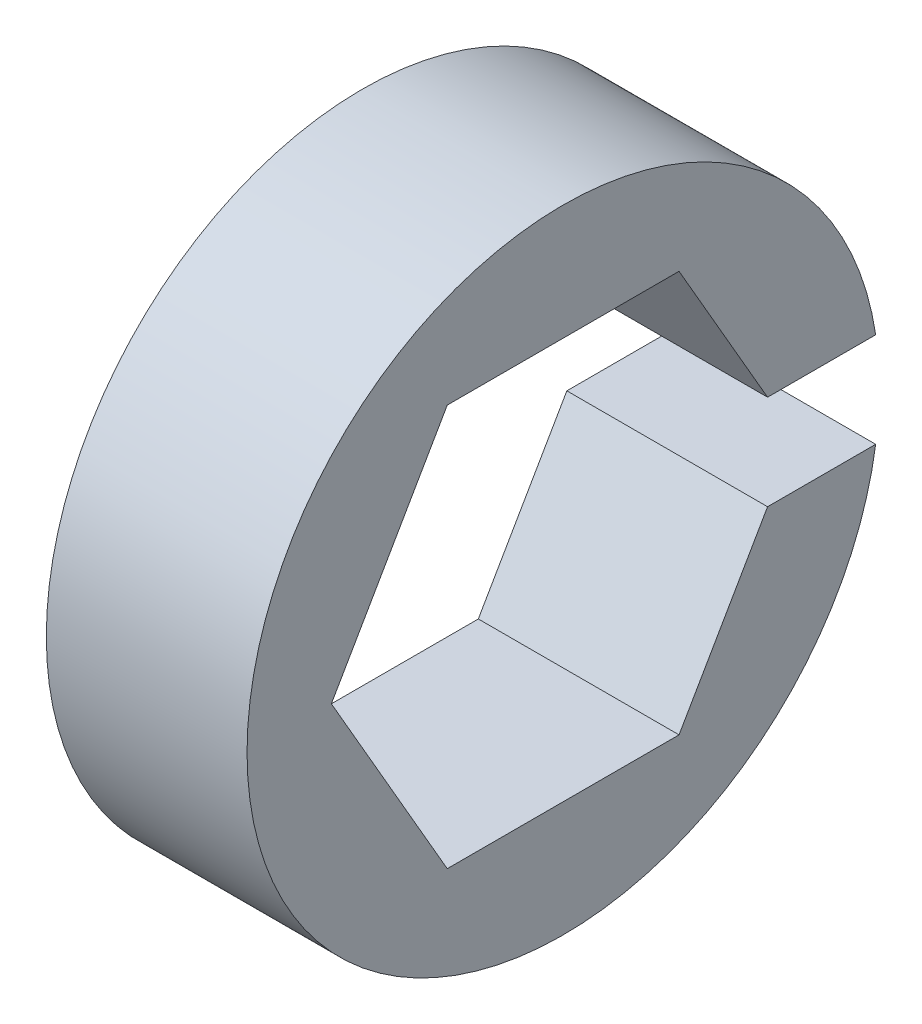
SolidWorks part; units mm, degrees
ref_plane "Front Plane" through (0, 0, 0) normal (0, 0, 1) x (1, 0, 0)
ref_plane "Top Plane" through (0, 0, 0) normal (0, 1, 0) x (1, 0, 0)
ref_plane "Right Plane" through (0, 0, 0) normal (1, 0, 0) x (0, 0, -1)
sketch "Sketch1" plane through (0, 0, 0) normal (1, 0, 0) x (0, 0, -1)
  line L1 (7.3323, 0) -> (3.6662, 6.35)
  line L2 (3.6662, 6.35) -> (-3.6662, 6.35)
  line L3 (-3.6662, 6.35) -> (-7.3323, 0)
  line L4 (-7.3323, 0) -> (-3.6662, -6.35)
  line L5 (-3.6662, -6.35) -> (3.6662, -6.35)
  line L6 (3.6662, -6.35) -> (7.3323, 0)
  circle A0 centre (0, 0) radius 10
  circle A1 centre (0, 0) radius 6.35 construction
  dimension "D2" = 20
  dimension "D1" = 12.7
extrude "Boss-Extrude1" add sketch "Sketch1" along normal blind 6.35
sketch "Sketch2" plane through (6.35, 0, 0) normal (1, 0, 0) x (0, 0, -1)
  line L1 (5.8102, 1.5) -> (11.4103, 1.5)
  line L2 (5.8102, 1.5) -> (5.8102, -1.5)
  line L3 (5.8102, -1.5) -> (11.4103, -1.5)
  line L4 (11.4103, 1.5) -> (11.4103, -1.5)
  point P4 (11.4103, 0)
  dimension "D1" = 3
extrude "Cut-Extrude1" cut sketch "Sketch2" against normal through all
